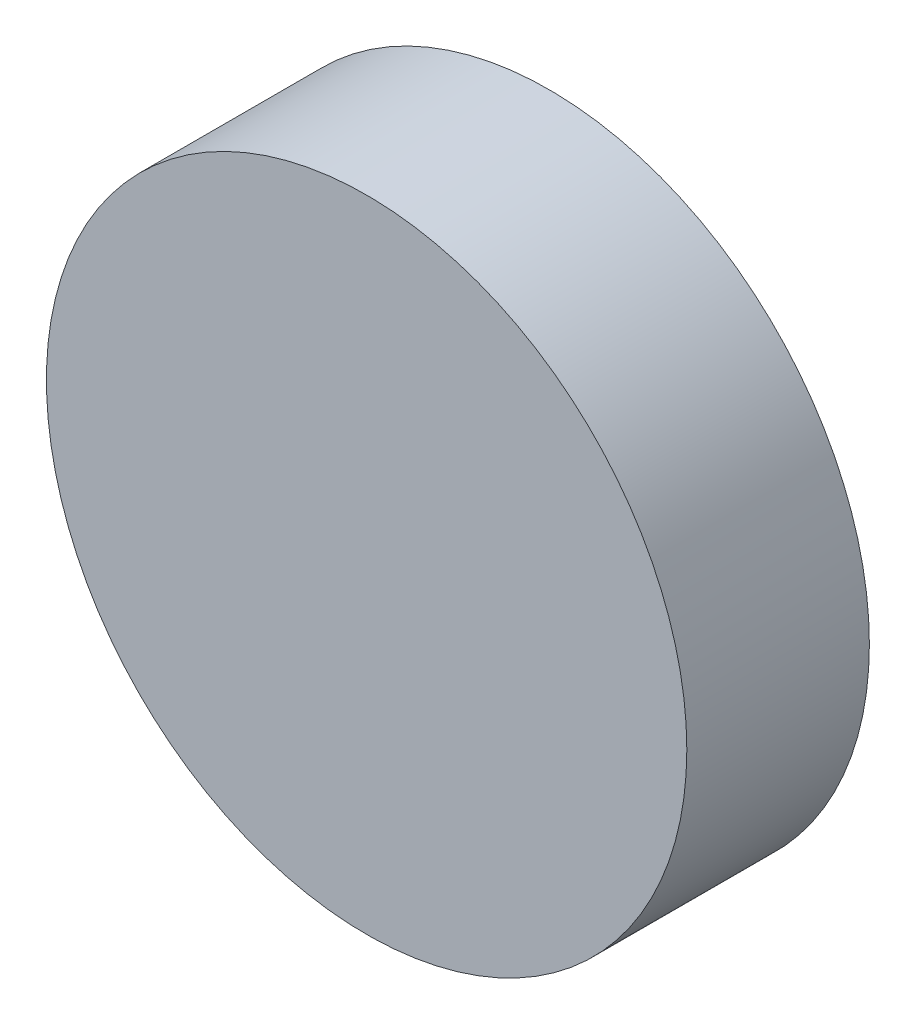
SolidWorks part; units mm, degrees
ref_plane "Ebene vorne" through (0, 0, 0) normal (0, 0, 1) x (1, 0, 0)
ref_plane "Ebene oben" through (0, 0, 0) normal (0, 1, 0) x (1, 0, 0)
ref_plane "Ebene rechts" through (0, 0, 0) normal (1, 0, 0) x (0, 0, -1)
sketch "Skizze1" plane through (0, 0, 0) normal (0, 0, 1) x (1, 0, 0)
  circle A0 centre (0, 0) radius 87.6977
extrude "Aufsatz-Linear austragen1" add sketch "Skizze1" along normal blind 50
